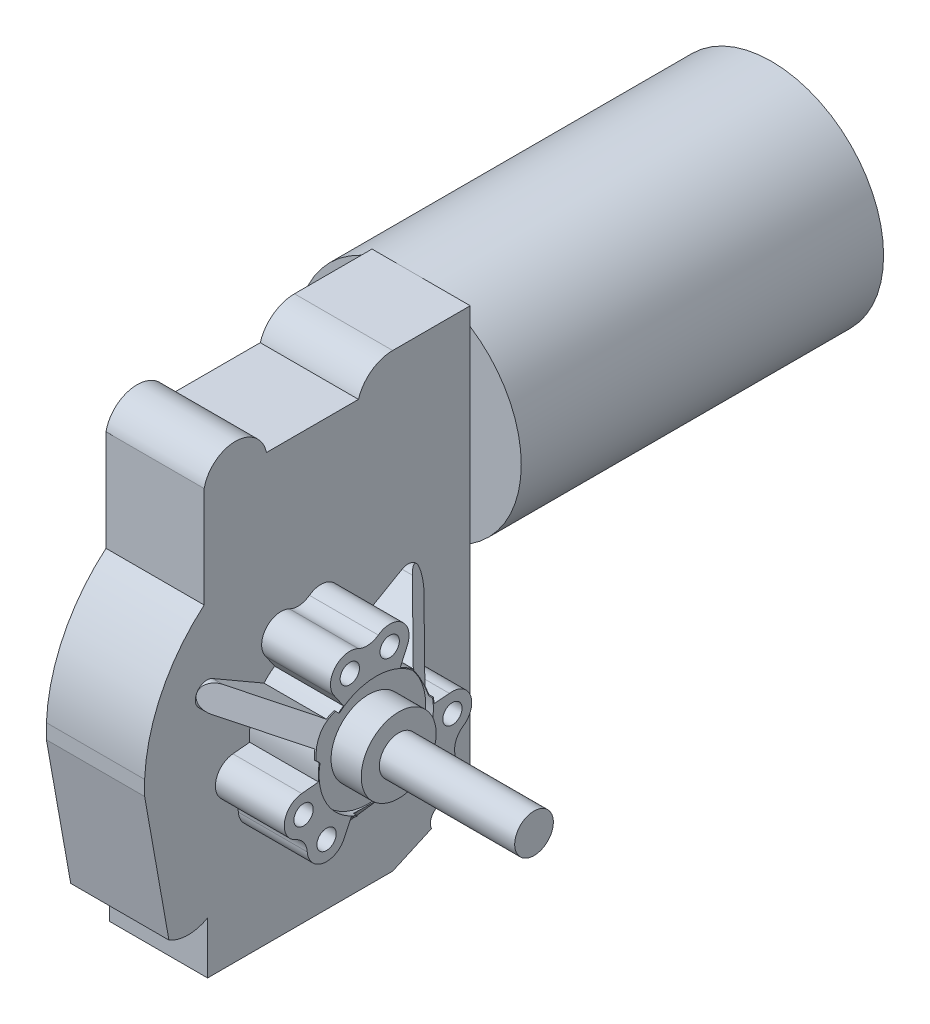
SolidWorks part; units mm, degrees
ref_plane "Front Plane" through (0, 0, 0) normal (0, 0, 1) x (1, 0, 0)
ref_plane "Top Plane" through (0, 0, 0) normal (0, 1, 0) x (1, 0, 0)
ref_plane "Right Plane" through (0, 0, 0) normal (1, 0, 0) x (0, 0, -1)
sketch "Sketch1" plane through (0, 0, 0) normal (0, 0, 1) x (1, 0, 0)
  circle A0 centre (0, 0) radius 36.83
  dimension "D1" = 73.66
extrude "Boss-Extrude1" add sketch "Sketch1" along normal blind 118.999
sketch "Sketch2" plane through (0, 0, 118.999) normal (0, 0, 1) x (1, 0, 0)
  line L0 (0, 0) -> (0, -111.252) construction
  line L1 (-17.272, -111.252) -> (0, -111.252)
  line L2 (-17.272, -111.252) -> (-17.272, 36.83)
  line L3 (-17.272, 36.83) -> (0, 36.83)
  line L4 (20.066, -111.252) -> (20.066, 36.83)
  line L5 (0, 0) -> (0, 36.83) construction
  line L6 (0, 36.83) -> (20.066, 36.83)
  line L7 (0, -111.252) -> (20.066, -111.252)
  point P0 (0, 0)
  dimension "D1" = 36.83
  dimension "D2" = 111.252
  dimension "D3" = 17.272
  dimension "D4" = 20.066
extrude "Boss-Extrude2" add sketch "Sketch2" along normal blind 106.934
sketch "Sketch5" plane through (0, 0, 0) normal (1, 0, 0) x (0, 0, -1)
  line L0 (-172.466, 36.83) -> (-172.466, -111.252) construction
  line L1 (-225.933, 36.83) -> (-118.999, 36.83) construction
  line L2 (-225.933, -111.252) -> (-118.999, -111.252) construction
  line L3 (-247.0561, -49.276) -> (-85.3382, -49.276) construction
  line L4 (-258.8324, -9.0027) -> (-172.466, -49.276) construction
  line L5 (-172.466, -49.276) -> (-73.227, -95.5519) construction
  line L6 (-172.466, -49.276) -> (-99.6291, -110.3934) construction
  line L7 (-172.466, -49.276) -> (-80.3, -65.5274) construction
  line L8 (-158.1767, -69.2923) -> (-161.3975, -64.7806)
  line L9 (-153.473, -47.8035) -> (-148.4306, -47.4125)
  line L10 (-180.6873, -66.4607) -> (-182.8699, -71.023)
  line L11 (-196.9453, -51.6428) -> (-191.4276, -51.1093)
  line L12 (-183.2377, -33.5638) -> (-186.0975, -29.3925)
  line L13 (-162.276, -26.8929) -> (-164.5729, -31.9381)
  line L14 (-172.466, -49.276) -> (-139.4704, -30.226) construction
  line L15 (-172.466, -49.276) -> (-139.4704, -30.226) construction
  line L16 (-168.656, -67.9411) -> (-168.656, -87.376)
  line L17 (-176.276, -67.9411) -> (-176.276, -87.376)
  line L18 (-154.3965, -43.243) -> (-137.5654, -33.5256)
  line L19 (-158.2065, -36.6439) -> (-141.3754, -26.9264)
  line L20 (-190.5355, -43.243) -> (-207.3666, -33.5256)
  line L21 (-186.7255, -36.6439) -> (-203.5566, -26.9264)
  arc A0 (-153.473, -47.8035) -> (-154.3965, -43.243) centre (-172.466, -49.276) ccw
  circle A1 centre (-153.0085, -65.6028) radius 3.175
  circle A2 centre (-147.4519, -53.6867) radius 3.175
  arc A3 (-158.1767, -69.2923) -> (-146.6953, -64.9199) centre (-153.0085, -65.6028) ccw
  arc A4 (-143.917, -58.9618) -> (-148.4306, -47.4125) centre (-147.4519, -53.6867) ccw
  arc A5 (-143.917, -58.9618) -> (-146.6953, -64.9199) centre (-140.3821, -64.237) ccw
  arc A6 (-195.1287, -69.1572) -> (-182.8699, -71.023) centre (-188.7928, -68.7335) ccw
  arc A7 (-196.9453, -51.6428) -> (-198.8993, -63.7721) centre (-196.3342, -57.9633) ccw
  arc A8 (-195.1287, -69.1572) -> (-198.8993, -63.7721) centre (-201.4645, -69.581) ccw
  circle A9 centre (-188.7928, -68.7335) radius 3.175
  circle A10 centre (-196.3342, -57.9633) radius 3.175
  arc A11 (-178.3523, -19.7089) -> (-186.0975, -29.3925) centre (-181.1533, -25.4078) ccw
  arc A12 (-162.276, -26.8929) -> (-171.8034, -19.136) centre (-168.0553, -24.2619) ccw
  arc A13 (-178.3523, -19.7089) -> (-171.8034, -19.136) centre (-175.5514, -14.0101) ccw
  circle A14 centre (-181.1533, -25.4078) radius 3.175
  circle A15 centre (-168.0553, -24.2619) radius 3.175
  arc A16 (-183.2377, -33.5638) -> (-186.7255, -36.6439) centre (-172.466, -49.276) ccw
  arc A17 (-180.6873, -66.4607) -> (-176.276, -67.9411) centre (-172.466, -49.276) ccw
  arc A18 (-158.2065, -36.6439) -> (-164.5729, -31.9381) centre (-172.466, -49.276) ccw
  arc A19 (-137.5654, -33.5256) -> (-141.3754, -26.9264) centre (-139.4704, -30.226) ccw
  arc A20 (-176.276, -87.376) -> (-168.656, -87.376) centre (-172.466, -87.376) ccw
  arc A21 (-203.5566, -26.9264) -> (-207.3666, -33.5256) centre (-205.4616, -30.226) ccw
  arc A22 (-189.7312, -41.2251) -> (-191.4276, -51.1093) centre (-172.466, -49.276) ccw
  arc A23 (-168.656, -67.9411) -> (-161.3975, -64.7806) centre (-172.466, -49.276) ccw
  point P9 (-155.9682, -39.751)
  point P49 (-172.466, -49.276)
  point P66 (-172.466, -49.276)
  dimension "D2" = 38.1
  dimension "D8" = 6.35
  dimension "D9" = 12.7
  dimension "D10" = 12.7
  dimension "D14" = 3.81
  dimension "D1" = 86.106
  dimension "D3" = 25
  dimension "D4" = 30
  dimension "D5" = 15
  dimension "D6" = 25.4
  dimension "D7" = 25.4
  dimension "D12" = 30
  dimension "D13" = 38.1
  dimension "D11" = 3
  dimension "D15" = 3
extrude "Boss-Extrude3" add sketch "Sketch5" along normal blind 42.672
sketch "Sketch6" plane through (42.672, 0, 0) normal (1, 0, 0) x (0, 0, -1)
  circle A0 centre (-172.466, -49.276) radius 12.3063
  dimension "D1" = 24.6126
extrude "Boss-Extrude4" add sketch "Sketch6" along normal blind 7.366
sketch "Sketch7" plane through (50.038, 0, 0) normal (1, 0, 0) x (0, 0, -1)
  circle A0 centre (-172.466, -49.276) radius 6.35
  dimension "D1" = 12.7
extrude "Boss-Extrude5" add sketch "Sketch7" along normal blind 44.45
ref_plane "Plane1" through (0, 0, 172.466) normal (0, 0, 1) x (1, 0, 0)
sketch "Sketch8" plane through (0, 0, 172.466) normal (0, 0, 1) x (1, 0, 0)
  line L1 (20.066, -91.186) -> (42.672, -91.186) construction
  line L2 (33.9845, -91.186) -> (42.672, -91.186)
  line L3 (42.672, -91.186) -> (42.672, -65.5585)
  line L4 (42.672, -65.5585) -> (20.066, -91.186)
  line L5 (20.066, -111.252) -> (20.066, 36.83) construction
  line L6 (20.066, -91.186) -> (33.9845, -91.186)
extrude "Cut-Extrude1" cut sketch "Sketch8" against normal mid plane 12.7
pattern_circular "CirPattern1" count 3 over 360 about axis through (0, -49.276, 172.466) along (1, 0, 0) of "Cut-Extrude1"
sketch "Sketch9" plane through (42.672, 0, 0) normal (1, 0, 0) x (0, 0, -1)
  circle A0 centre (-172.466, -49.276) radius 18.7785
  circle A1 centre (-172.466, -49.276) radius 12.3063
extrude "Cut-Extrude3" cut sketch "Sketch9" against normal blind 2.54
sketch "Sketch10" plane through (20.066, 0, 0) normal (1, 0, 0) x (0, 0, -1)
  line L0 (0, 0) -> (-225.933, 0) construction
  line L1 (-172.466, -49.276) -> (-253.6869, -49.276) construction
  line L2 (-206.375, 28.5445) -> (-118.999, 28.5445) construction
  line L3 (-118.999, 30.8837) -> (-118.999, -30.8837) construction
  line L4 (-185.9053, 28.5445) -> (-155.6983, 28.5445)
  line L5 (-144.4628, 36.83) -> (-118.999, 36.83)
  line L6 (0, 36.83) -> (-118.999, 36.83) construction
  line L7 (-118.999, 30.8837) -> (-118.999, 36.83) construction
  line L8 (-118.999, 36.83) -> (-118.999, 50.6471)
  line L9 (-225.933, -111.252) -> (-225.933, 36.83) construction
  line L10 (-206.375, 28.5445) -> (-206.375, -4.6096)
  line L11 (-225.933, -49.276) -> (-217.9542, -94.1254)
  line L12 (-205.2542, -94.1254) -> (-205.2542, -111.252)
  line L13 (-225.933, -111.252) -> (-118.999, -111.252) construction
  line L14 (-205.2542, -111.252) -> (-144.4628, -111.252)
  line L15 (-144.4628, -111.252) -> (-131.7309, -105.5451)
  line L16 (-128.0784, -99.9052) -> (-118.999, -99.9052)
  line L17 (-118.999, -111.252) -> (-118.999, -30.8837) construction
  line L18 (-118.999, -99.9052) -> (-118.999, -36.83)
  line L19 (-118.999, -36.83) -> (-118.999, -30.8837) construction
  line L20 (-118.999, -36.83) -> (-97.863, -40.7106)
  line L21 (-97.863, -40.7106) -> (-101.1784, -130.5948)
  line L22 (-101.1784, -130.5948) -> (-248.1612, -133.5418)
  line L23 (-248.1612, -133.5418) -> (-241.4882, 47.3709)
  line L24 (-241.4882, 47.3709) -> (-118.999, 50.6471)
  line L25 (-118.999, 50.6471) -> (-117.387, 51.0155)
  arc A0 (-206.375, 28.5445) -> (-185.9053, 28.5445) centre (-196.1402, 26.3659) cw
  arc A1 (-155.6983, 28.5445) -> (-144.4628, 36.83) centre (-144.4628, 25.0693) cw
  arc A2 (-206.375, -4.6096) -> (-225.933, -49.276) centre (-170.6946, -46.848) ccw
  arc A3 (-217.9542, -94.1254) -> (-205.2542, -94.1254) centre (-211.6042, -83.1269) ccw
  arc A4 (-131.7309, -105.5451) -> (-128.0784, -99.9052) centre (-128.0784, -103.9079) cw
  line M36 (-118.999, -111.252) -> (-118.999, -30.8837)
  line M39 (-118.999, 36.83) -> (-225.933, 36.83)
  line M40 (-225.933, 36.83) -> (-225.933, -111.252)
  line M41 (-225.933, -111.252) -> (-118.999, -111.252)
  dimension "D2" = 12.7
  dimension "D1" = 33.909
  dimension "D3" = 12.7
extrude "Cut-Extrude5" cut sketch "Sketch10" against normal blind 64.516 contours L4 A1 A0 M39 | A2 L8 L24 L23 L22 L21 L20 M40 M39 M36 M41 | A2 L10 A0 M39 M40 | A3 L11 L12 M40 M41 | A4 L15 L16 M41 M36
sketch "Sketch11" plane through (-17.272, 0, 0) normal (-1, 0, 0) x (0, 0, 1)
  line L0 (225.933, -49.276) -> (118.999, -49.276) construction
  line L1 (118.999, -32.5289) -> (118.999, -99.9052) construction
  line L3 (225.933, -135.382) -> (118.999, -135.382)
  line L4 (225.933, -135.382) -> (225.933, 36.83)
  line L5 (225.933, 36.83) -> (118.999, 36.83)
  line L6 (118.999, -135.382) -> (118.999, 36.83)
  line L7 (225.933, -135.382) -> (118.999, 36.83) construction
  line L8 (225.933, 36.83) -> (118.999, -135.382) construction
  circle A0 centre (172.466, -49.276) radius 19.05
  dimension "D1" = 38.1
extrude "Cut-Extrude6" cut sketch "Sketch11" against normal blind 5.08
